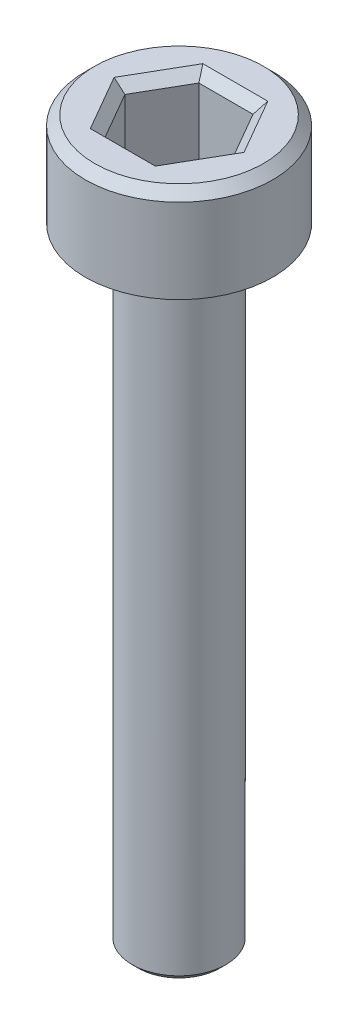
SolidWorks part; units mm, degrees
ref_plane "Front Plane" through (0, 0, 0) normal (0, 0, 1) x (1, 0, 0)
ref_plane "Top Plane" through (0, 0, 0) normal (0, 1, 0) x (1, 0, 0)
ref_plane "Right Plane" through (0, 0, 0) normal (1, 0, 0) x (0, 0, -1)
sketch "Sketch1" plane through (0, 0, 0) normal (0, 1, 0) x (1, 0, 0)
  circle A0 centre (0, 0) radius 3
  dimension "D1" = 6
extrude "Boss-Extrude1" add sketch "Sketch1" along normal blind 3
chamfer "Chamfer1" distance 0.3 angle 45 1 edges at (0, 3, 3)
sketch "Sketch2" plane through (0, 3, 0) normal (0, 1, 0) x (1, 0, 0)
  line L1 (1.7321, 0) -> (0.866, 1.5)
  line L2 (0.866, 1.5) -> (-0.866, 1.5)
  line L3 (-0.866, 1.5) -> (-1.7321, 0)
  line L4 (-1.7321, 0) -> (-0.866, -1.5)
  line L5 (-0.866, -1.5) -> (0.866, -1.5)
  line L6 (0.866, -1.5) -> (1.7321, 0)
  circle A0 centre (0, 0) radius 1.5 construction
  dimension "D1" = 3
extrude "Cut-Extrude1" cut sketch "Sketch2" against normal blind 2.5
chamfer "Chamfer2" distance 0.3 angle 45 6 edges at (1.299, 3, -0.75) (1.299, 3, 0.75) (0, 3, 1.5) (-1.299, 3, 0.75) (-1.299, 3, -0.75) (0, 3, -1.5)
sketch "Sketch3" plane through (0, 0, 0) normal (0, -1, 0) x (1, 0, 0)
  circle A0 centre (0, 0) radius 1.5
  dimension "D1" = 3
extrude "Boss-Extrude2" add sketch "Sketch3" along normal blind 20
chamfer "Chamfer3" distance 0.2 angle 45 1 edges at (0, -20, -1.5)
